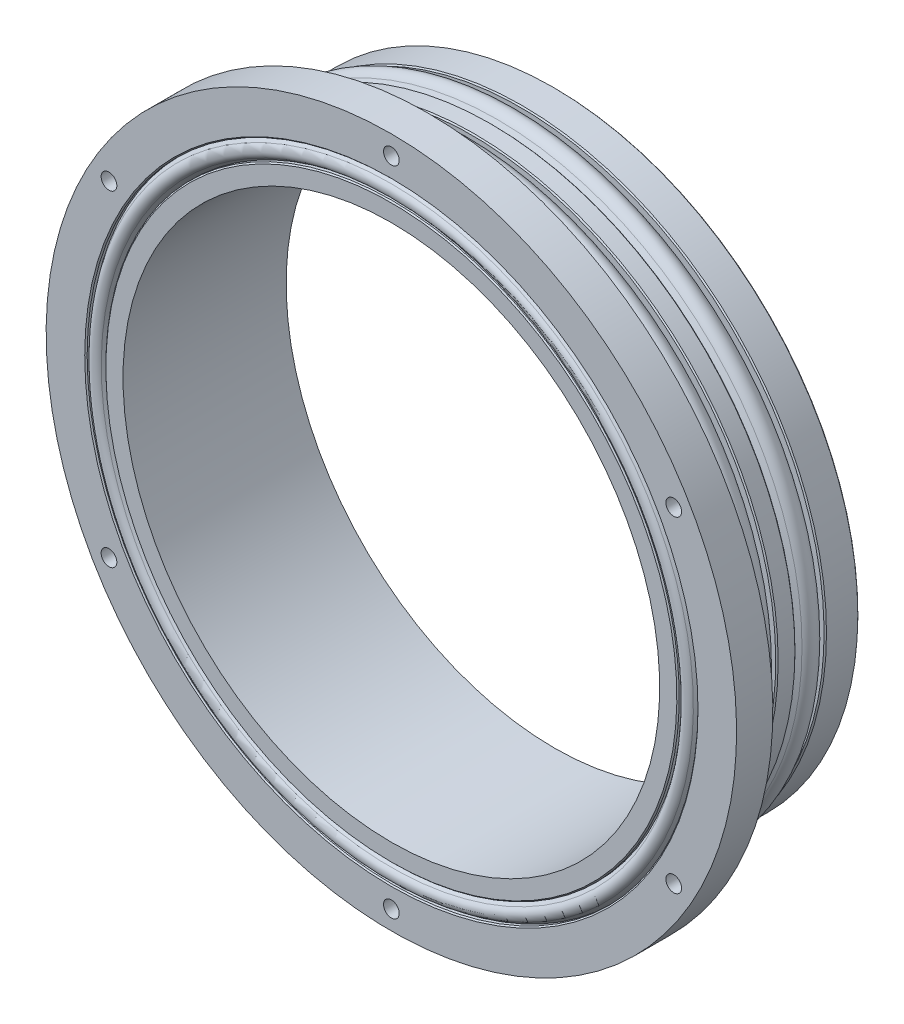
SolidWorks part; units mm, degrees
material "1060 Alloy"
ref_plane "Front Plane" through (0, 0, 0) normal (0, 0, 1) x (1, 0, 0)
ref_plane "Top Plane" through (0, 0, 0) normal (0, 1, 0) x (1, 0, 0)
ref_plane "Right Plane" through (0, 0, 0) normal (1, 0, 0) x (0, 0, -1)
sketch "Sketch1" plane through (0, 0, 0) normal (1, 0, 0) x (0, 0, -1)
  line L0 (0, 0) -> (0, 50.8) construction
  line L1 (0, 50.419) -> (-5.587, 50.419)
  line L2 (-21, 50.419) -> (-21, 57.15)
  line L3 (-21, 57.15) -> (-27, 57.15)
  line L4 (-27, 57.15) -> (-27, 50.5587)
  line L5 (-27, 44.419) -> (0, 44.419)
  line L6 (0, 44.419) -> (0, 50.419)
  line L7 (-18.413, 50.419) -> (-21, 50.419)
  line L8 (-10.413, 50.419) -> (-13.587, 50.419)
  line L9 (0, 0) -> (-27, 0) construction
  line L10 (-27, 0) -> (-27, 44.419) construction
  line L11 (-18.413, 50.419) -> (-18.413, 49.0411)
  line L12 (-26.2792, 50.5587) -> (-27.019, 50.0138)
  line L13 (-13.587, 49.0411) -> (-13.587, 50.419)
  line L14 (-10.413, 50.419) -> (-10.413, 49.0411)
  line L15 (-26.2792, 47.4599) -> (-27.019, 48.0048)
  line L16 (-5.587, 49.0411) -> (-5.587, 50.419)
  line L17 (0, 50.8) -> (-21, 50.8) construction
  line L18 (-16, 50.8) -> (-16, 51.1937) construction
  line L19 (-21, 50.4825) -> (0, 50.4825) construction
  line L20 (-27, 47.4599) -> (-26.2792, 47.4599)
  line L21 (-18.413, 49.0411) -> (-13.587, 49.0411) construction
  line L22 (-26.2792, 50.5587) -> (-27, 50.5587)
  line L23 (-27, 47.4599) -> (-27, 44.419)
  line L24 (0, 48.919) -> (-4, 48.919) construction
  line L25 (-4, 48.919) -> (-4, 45.919) construction
  line L26 (-4, 45.919) -> (0, 45.919) construction
  line L27 (-4, 47.419) -> (0, 47.419) construction
  line L28 (-18.413, 49.0411) -> (-17.4525, 50.4317)
  line L29 (-13.587, 49.0411) -> (-14.5475, 50.4317)
  line L30 (-10.413, 49.0411) -> (-9.4525, 50.4317)
  line L31 (-5.587, 49.0411) -> (-6.5475, 50.4317)
  line L32 (-10.413, 49.0411) -> (-5.587, 49.0411) construction
  line L33 (-26.2792, 50.5587) -> (-26.2792, 47.4599) construction
  arc A0 (-14.5475, 50.4317) -> (-17.4525, 50.4317) centre (-16, 49.4284) ccw
  arc A1 (-6.5475, 50.4317) -> (-9.4525, 50.4317) centre (-8, 49.4284) ccw
  arc A2 (-27.019, 50.0138) -> (-27.019, 48.0048) centre (-26.2792, 49.0093) ccw
  point P21 (-27.5267, 49.0093)
  dimension "D4" = 3.5306
  dimension "D12" = 2.587
  dimension "D15" = 0.3873
  dimension "D24" = 1.2475
  dimension "D1" = 50.8
  dimension "D2" = 100.838
  dimension "D3" = 6
  dimension "D5" = 21
  dimension "D6" = 6
  dimension "D7" = 57.15
  dimension "D8" = 4.826
  dimension "D9" = 8
  dimension "D10" = 8
  dimension "D11" = 1.378
  dimension "D13" = 3.174
  dimension "D14" = 50.4825
  dimension "D16" = 0.127
  dimension "D17" = 0.762
  dimension "D18" = 3.0988
  dimension "D19" = 0.7208
  dimension "D20" = 94.9198
  dimension "D21" = 3.0409
  dimension "D22" = 3
  dimension "D23" = 4
revolve "Revolve1" add sketch "Sketch1" angle 360 about L9
sketch "Sketch2" plane through (0, 0, 27) normal (0, 0, 1) x (1, 0, 0)
  circle A0 centre (0, 53.975) radius 1.3
  circle A1 centre (0, 0) radius 57.15 construction
  circle A2 centre (46.7437, 26.9875) radius 1.3
  circle A3 centre (46.7437, -26.9875) radius 1.3
  circle A4 centre (0, -53.975) radius 1.3
  circle A5 centre (-46.7437, -26.9875) radius 1.3
  circle A6 centre (-46.7437, 26.9875) radius 1.3
  point P17 (0, 0)
  dimension "D1" = 2.6
  dimension "D2" = 3.175
  dimension "D3" = 6
extrude "Cut-Extrude1" cut sketch "Sketch2" against normal up to surface (6 mm away) up to face at (0, 57.15, 21)
chamfer "Chamfer1" distance 0.2 angle 45 7 edges at (0, 50.419, 18.413) (0, 50.419, 5.587) (0, 50.419, 10.413) (0, 50.419, 13.587) (0, 50.419, 0) (0, 50.5587, 27) (0, 47.4599, 27)
sketch "Sketch3" plane through (0, 0, 0) normal (0, 0, -1) x (-1, 0, 0)
  line L0 (-46.99, 0) -> (0, 0) construction
  line L1 (0, 0) -> (0, 46.99) construction
  line L2 (0, 0) -> (46.99, 0) construction
  line L3 (0, -46.99) -> (0, 0) construction
  circle A0 centre (-46.99, 0) radius 1.3
  circle A1 centre (0, 46.99) radius 1.3
  circle A2 centre (46.99, 0) radius 1.3
  circle A3 centre (0, -46.99) radius 1.3
  circle A4 centre (-46.99, 0) radius 2.75 construction
  dimension "D2" = 5.5
  dimension "D3" = 2.6
  dimension "D1" = 93.98
extrude "Cut-Extrude2" cut sketch "Sketch3" against normal blind 4
